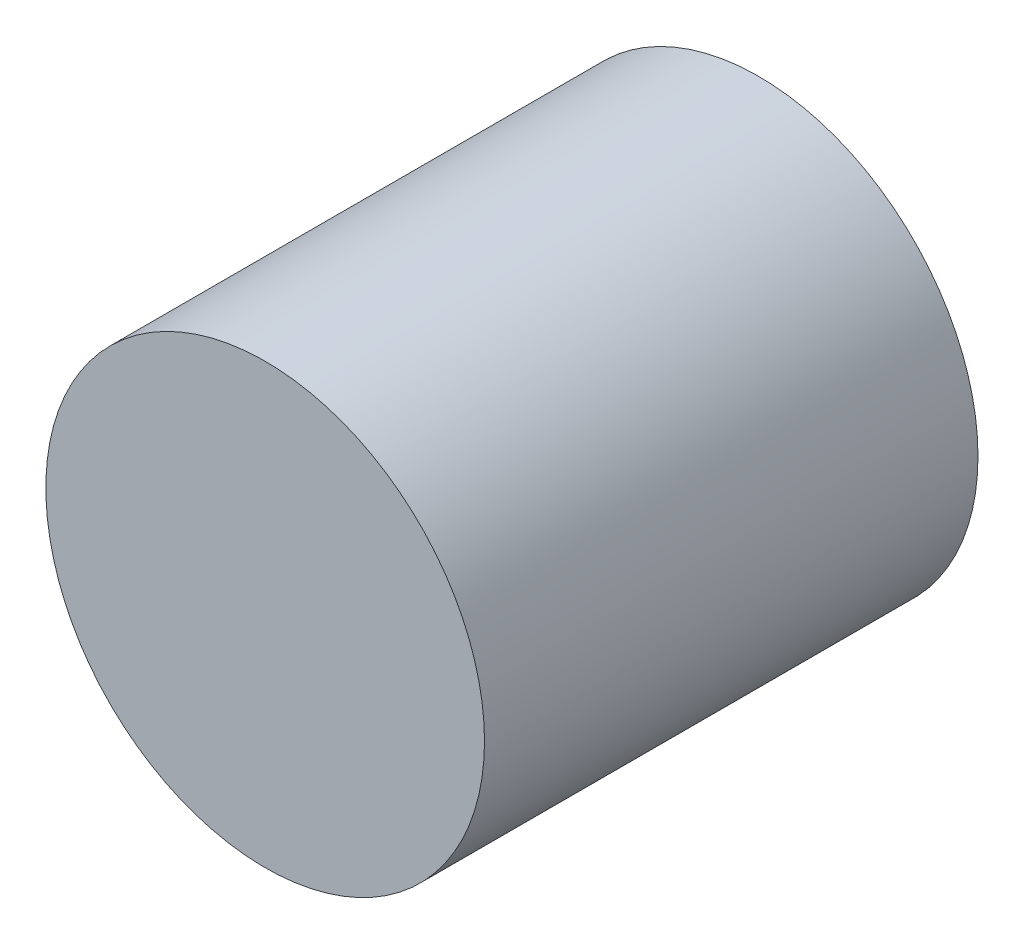
SolidWorks part; units mm, degrees
ref_plane "前基準面" through (0, 0, 0) normal (0, 0, 1) x (1, 0, 0)
ref_plane "上基準面" through (0, 0, 0) normal (0, 1, 0) x (1, 0, 0)
ref_plane "右基準面" through (0, 0, 0) normal (1, 0, 0) x (0, 0, -1)
sketch "草圖1" plane through (0, 0, 0) normal (0, 0, 1) x (1, 0, 0)
  circle A0 centre (0, 0) radius 4
  dimension "D1" = 8
extrude "填料-伸長1" add sketch "草圖1" along normal mid plane 9
